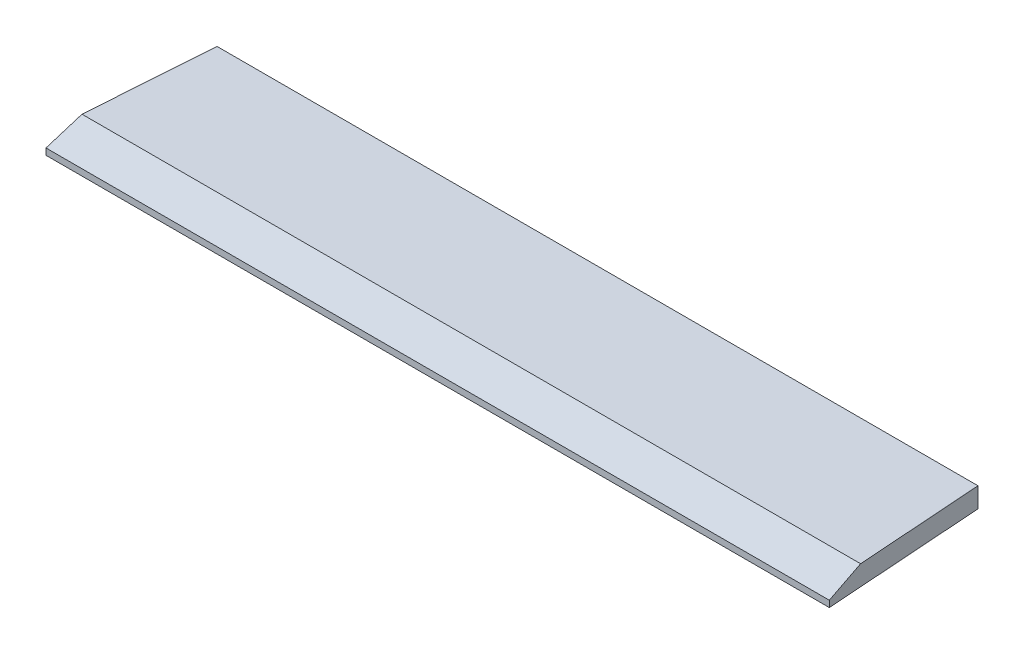
SolidWorks part; units mm, degrees
material "MS-Bis 400"
ref_plane "Front Plane" through (0, 0, 0) normal (0, 0, 1) x (1, 0, 0)
ref_plane "Top Plane" through (0, 0, 0) normal (0, 1, 0) x (1, 0, 0)
ref_plane "Right Plane" through (0, 0, 0) normal (1, 0, 0) x (0, 0, -1)
sketch "Sketch1" plane through (0, 0, 0) normal (1, 0, 0) x (0, 0, -1)
  line L0 (-200, -7) -> (-200, -15)
  line L1 (-200, -15) -> (0, -15)
  line L2 (0, -15) -> (0, 10)
  line L3 (0, 10) -> (-157.9235, 10)
  line L4 (-157.9235, 10) -> (-200, -7)
  dimension "D1" = 200
  dimension "D2" = 8
  dimension "D3" = 22
  dimension "D4" = 25
  dimension "D5" = 42.0765
  dimension "D6" = 10
extrude "Extrude1" add sketch "Sketch1" along normal mid plane 980
sketch "Sketch2" plane through (0, 0, 0) normal (0, 1, 0) x (1, 0, 0)
  line L0 (-476.0146, 0) -> (-490, -200)
  line L1 (490, -200) -> (-490, -200) construction
  line L2 (490, 0) -> (-490, 0) construction
  dimension "D1" = 86
extrude "Cut-Extrude1" cut sketch "Sketch2" against normal through all and the other way through all flip side to cut
sketch "Sketch3" plane through (0, 0, 0) normal (0, 1, 0) x (1, 0, 0)
  line L0 (490, -200) -> (476.0146, 0)
  line L1 (490, 0) -> (-476.0146, 0) construction
  line L2 (490, -200) -> (-490, -200) construction
  dimension "D1" = 86
extrude "Cut-Extrude2" cut sketch "Sketch3" against normal through all and the other way through all flip side to cut
